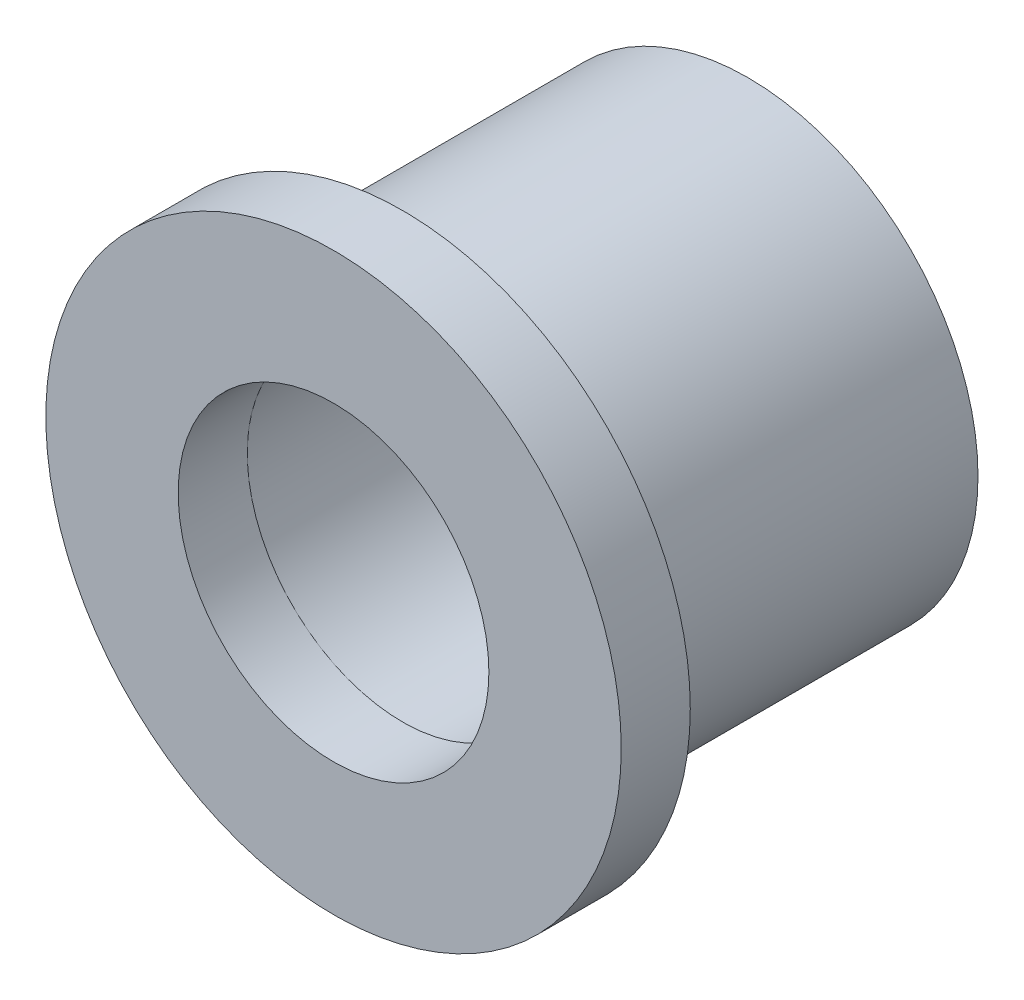
SolidWorks part; units mm, degrees
ref_plane "Front Plane" through (0, 0, 0) normal (0, 0, 1) x (1, 0, 0)
ref_plane "Top Plane" through (0, 0, 0) normal (0, 1, 0) x (1, 0, 0)
ref_plane "Right Plane" through (0, 0, 0) normal (1, 0, 0) x (0, 0, -1)
sketch "Sketch1" plane through (0, 0, 0) normal (0, 0, 1) x (1, 0, 0)
  circle A0 centre (0, 0) radius 8.5725
  circle A1 centre (0, 0) radius 15.875
  dimension "D1" = 31.75
  dimension "D2" = 17.145
extrude "Boss-Extrude1" add sketch "Sketch1" along normal blind 3.81
sketch "Sketch2" plane through (0, 0, 0) normal (0, 0, -1) x (-1, 0, 0)
  circle A0 centre (0, 0) radius 12.7
  circle A1 centre (0, 0) radius 8.636
  dimension "D1" = 25.4
  dimension "D2" = 17.272
extrude "Boss-Extrude2" add sketch "Sketch2" along normal blind 19.05
